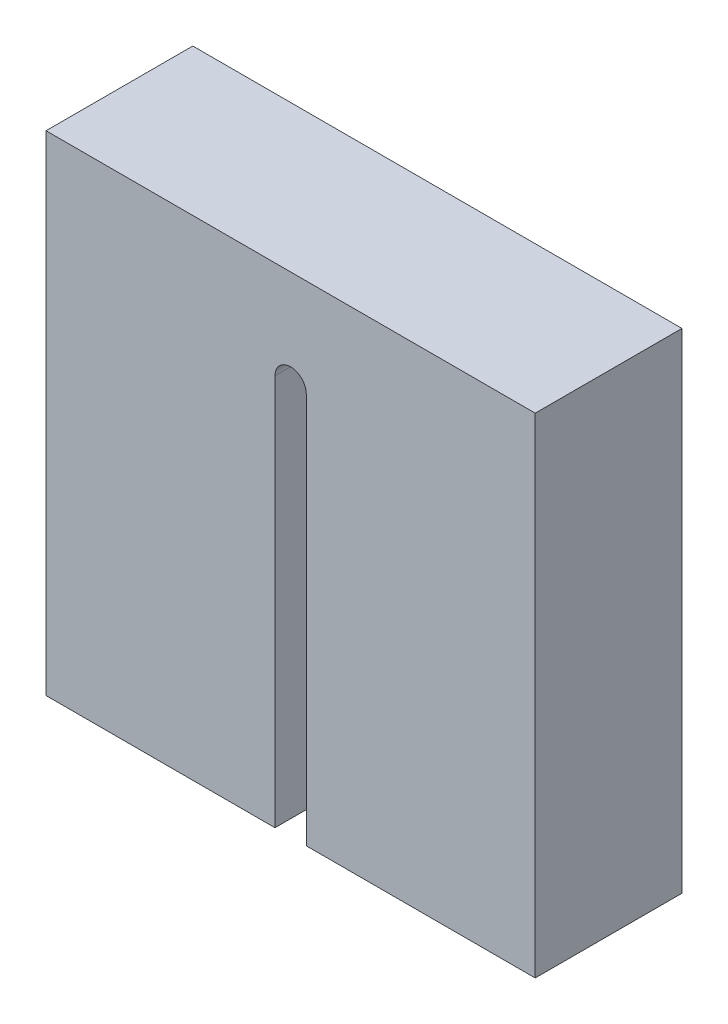
SolidWorks part; units mm, degrees
ref_plane "Plan de face" through (0, 0, 0) normal (0, 0, 1) x (1, 0, 0)
ref_plane "Plan de dessus" through (0, 0, 0) normal (0, 1, 0) x (1, 0, 0)
ref_plane "Plan de droite" through (0, 0, 0) normal (1, 0, 0) x (0, 0, -1)
sketch "Esquisse1" plane through (0, 0, 0) normal (0, 0, 1) x (1, 0, 0)
  line L0 (17.9177, 25) -> (30.2033, 25) construction
  line L1 (0, 0) -> (23.4, 0)
  line L2 (0, 0) -> (0, 50)
  line L3 (0, 50) -> (50, 50)
  line L4 (50, 0) -> (50, 50)
  line L5 (25, 82.493) -> (25, -3.859) construction
  line L6 (23.4, 40) -> (23.4, 0)
  line L7 (23.4, 45.4102) -> (23.4, -3.859) construction
  line L8 (26.6, 45.4102) -> (26.6, -3.859) construction
  line L9 (19.0214, 40) -> (31.293, 40) construction
  line L10 (26.6, 40) -> (26.6, 0)
  line L11 (26.6, 0) -> (50, 0)
  arc A1 (23.4, 40) -> (26.6, 40) centre (25, 40) cw
extrude "Extrusion1" add sketch "Esquisse1" along normal blind 15
